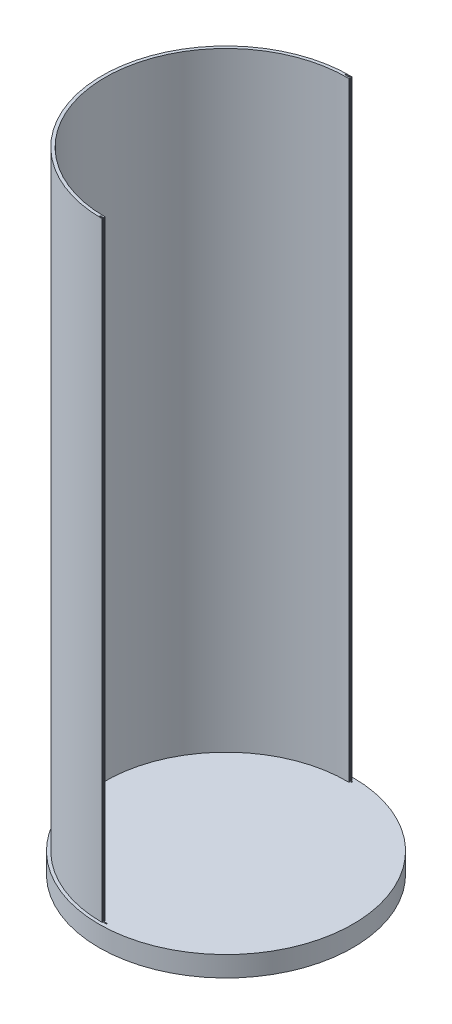
SolidWorks part; units mm, degrees
ref_plane "Front Plane" through (0, 0, 0) normal (0, 0, 1) x (1, 0, 0)
ref_plane "Top Plane" through (0, 0, 0) normal (0, 1, 0) x (1, 0, 0)
ref_plane "Right Plane" through (0, 0, 0) normal (1, 0, 0) x (0, 0, -1)
sketch "Sketch1" plane through (0, 0, 0) normal (0, 1, 0) x (1, 0, 0)
  circle A0 centre (0, 0) radius 62.5
  circle A1 centre (0, 0) radius 59.5
  dimension "D1" = 125
  dimension "D2" = 3
extrude "Boss-Extrude2" add sketch "Sketch1" along normal blind 10 contours A0
ref_plane "Plane1" through (0, 10, 0) normal (0, 1, 0) x (1, 0, 0)
sketch "Sketch4" plane through (0, 10, 0) normal (0, 1, 0) x (1, 0, 0)
  line L0 (0, -61) -> (0, -62.5)
  line L1 (0, 62.5) -> (0, 61)
  arc A0 (0, 62.5) -> (0, -62.5) centre (0, 0) ccw
  circle A1 centre (0, 0) radius 62.5 construction
  arc A2 (1, 59.4916) -> (0, -59.5) centre (0, 0) ccw
  arc A3 (0, 61) -> (0, -61) centre (0, 0) ccw
  circle A4 centre (0, 0) radius 61
  circle A5 centre (0, 0) radius 59.5
  arc A6 (0, 59.5) -> (0, -59.5) centre (0, 0) ccw construction
  dimension "D3" = 179.037
  dimension "D1" = 3
  dimension "D2" = 1.5
extrude "Extrude-Thin1" add sketch "Sketch4" along normal blind 300 thin contours A2
sketch "Sketch7" plane through (0, 10, 0) normal (0, 1, 0) x (1, 0, 0)
  arc A0 (-2.5955, -62.4461) -> (-3.7429, -62.3878) centre (0, 0) cw
  circle A1 centre (0, 0) radius 62.5 construction
  dimension "D1" = 62.5
sketch "Sketch8" plane through (0, 310, 0) normal (0, 1, 0) x (1, 0, 0)
  line L1 (-1.6257, -60.1397) -> (1.7115, -60.1397)
  line L2 (-1.6257, -60.1397) -> (-1.6257, -60.6217)
  line L3 (-1.6257, -60.6217) -> (1.7115, -60.6217)
  line L4 (1.7115, -60.1397) -> (1.7115, -60.6217)
extrude "Cut-Extrude1" cut sketch "Sketch8" against normal through all
mirror "Mirror1" about plane through (0, 0, 0) normal (0, 0, 1) of "Cut-Extrude1"
